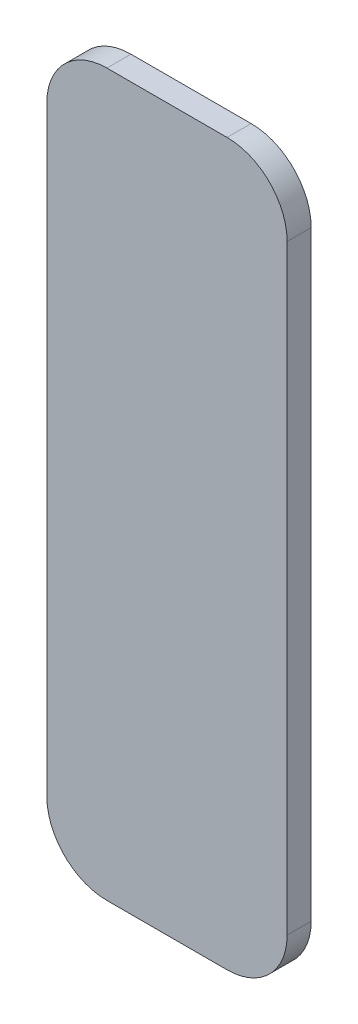
SolidWorks part; units mm, degrees
ref_plane "Front Plane" through (0, 0, 0) normal (1, 0, 0) x (0, 1, 0)
ref_plane "Top Plane" through (0, 0, 0) normal (0, 0, 1) x (0, 1, 0)
ref_plane "Right Plane" through (0, 0, 0) normal (0, 1, 0) x (-1, 0, 0)
sketch "Sketch1" plane through (0, 0, 0) normal (0, 0, 1) x (0, 1, 0)
  line L1 (6.35, 0) -> (69.85, 0)
  line L2 (0, 6.35) -> (0, 19.05)
  line L3 (6.35, 25.4) -> (69.85, 25.4)
  line L4 (76.2, 6.35) -> (76.2, 19.05)
  arc A0 (0, 6.35) -> (6.35, 0) centre (6.35, 6.35) ccw
  arc A1 (69.85, 0) -> (76.2, 6.35) centre (69.85, 6.35) ccw
  arc A2 (76.2, 19.05) -> (69.85, 25.4) centre (69.85, 19.05) ccw
  arc A3 (6.35, 25.4) -> (0, 19.05) centre (6.35, 19.05) ccw
  point P7 (0, 0)
  point P12 (76.2, 25.4)
  point P15 (0, 25.4)
  dimension "D3" = 6.35
  dimension "D1" = 76.2
  dimension "D2" = 25.4
extrude "Boss-Extrude1" add sketch "Sketch1" along normal blind 2.54
